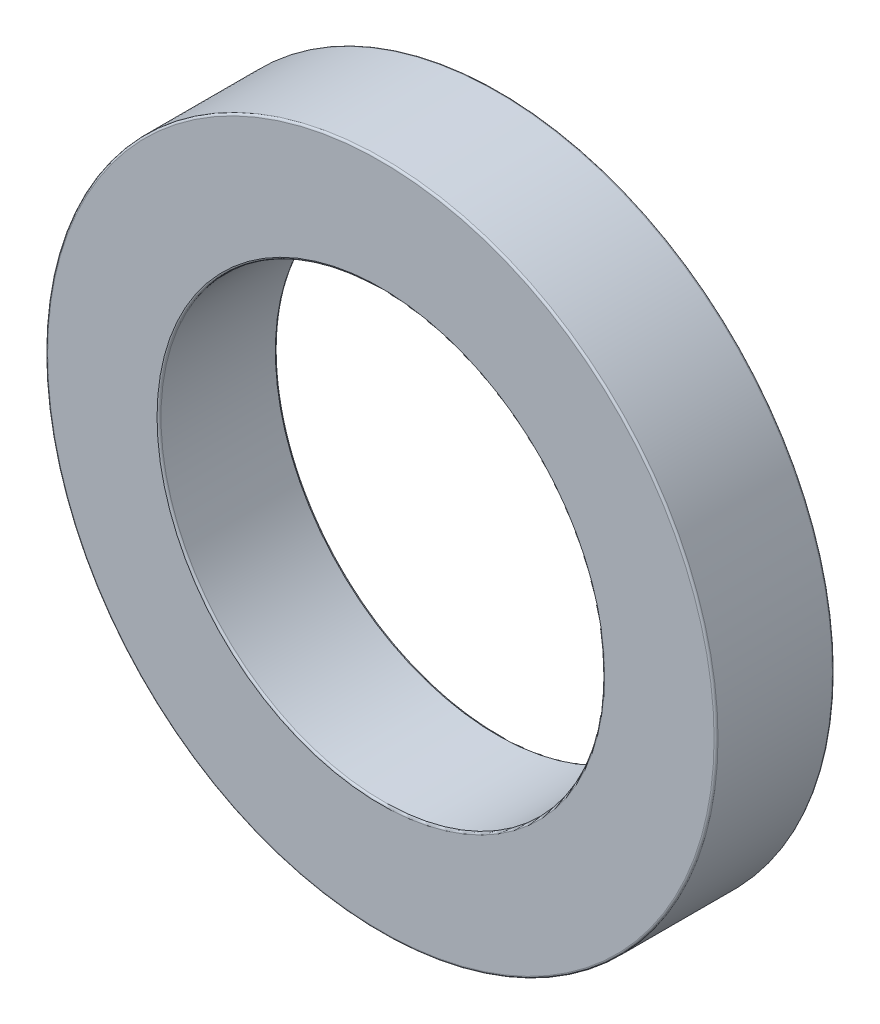
SolidWorks part; units mm, degrees
material "7075-T6 (SN)"
ref_plane "정면" through (0, 0, 0) normal (0, 0, 1) x (1, 0, 0)
ref_plane "윗면" through (0, 0, 0) normal (0, 1, 0) x (1, 0, 0)
ref_plane "우측면" through (0, 0, 0) normal (1, 0, 0) x (0, 0, -1)
sketch "스케치1" plane through (0, 0, 0) normal (0, 0, 1) x (1, 0, 0)
  circle A0 centre (0, 0) radius 22.5
  circle A1 centre (0, 0) radius 34
  dimension "D1" = 68
  dimension "D2" = 45
extrude "보스-돌출1" add sketch "스케치1" along normal blind 12
fillet "필렛1" radius 0.2 4 edges at (34, 0, 0) (34, 0, 12) (22.5, 0, 0) (22.5, 0, 12)
